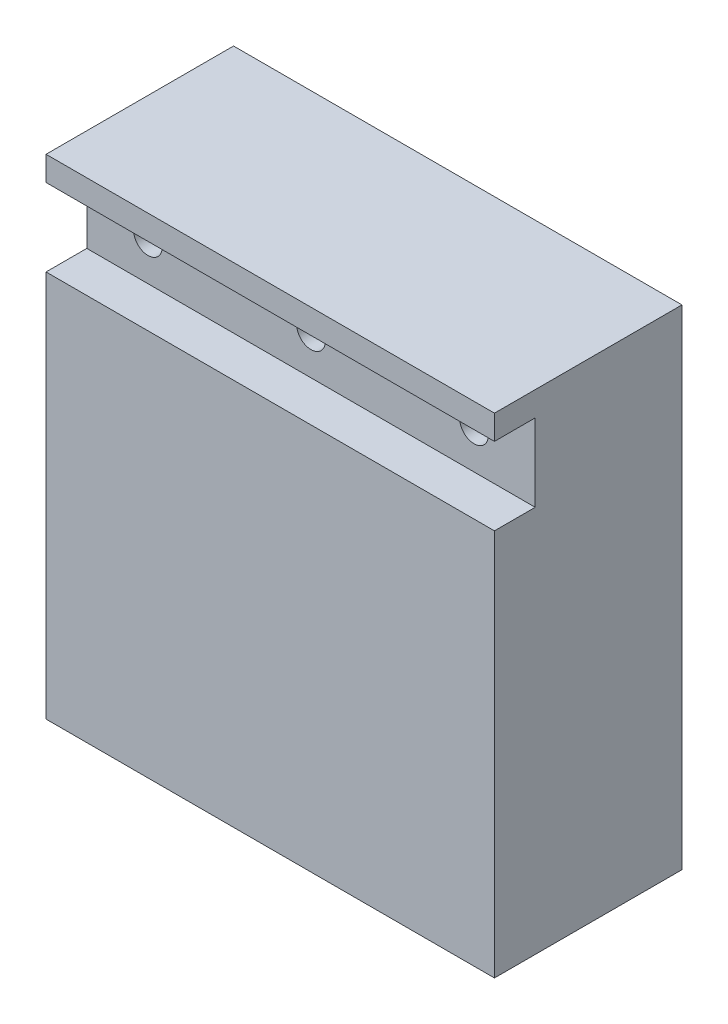
SolidWorks part; units mm, degrees
ref_plane "Front Plane" through (0, 0, 0) normal (0, 0, 1) x (1, 0, 0)
ref_plane "Top Plane" through (0, 0, 0) normal (0, 1, 0) x (1, 0, 0)
ref_plane "Right Plane" through (0, 0, 0) normal (1, 0, 0) x (0, 0, -1)
sketch "Sketch1" plane through (0, 0, 0) normal (1, 0, 0) x (0, 0, -1)
  line L1 (0, 0) -> (23, 0)
  line L2 (0, 0) -> (0, 60)
  line L3 (0, 60) -> (23, 60)
  line L4 (23, 0) -> (23, 60)
  dimension "D1" = 60
  dimension "D2" = 23
extrude "Boss-Extrude1" add sketch "Sketch1" along normal blind 55
sketch "Sketch2" plane through (0, 0, 0) normal (0, 0, 1) x (1, 0, 0)
  line L0 (55, 60) -> (55, 0) construction
  line L1 (0, 57) -> (55, 57)
  line L2 (0, 57) -> (0, 47.5)
  line L3 (0, 47.5) -> (55, 47.5)
  line L4 (55, 57) -> (55, 47.5)
  line L5 (55, 60) -> (0, 60) construction
  dimension "D1" = 9.5
  dimension "D2" = 3
  dimension "D3" = 55
extrude "Cut-Extrude1" cut sketch "Sketch2" against normal blind 5
sketch "Sketch3" plane through (0, 0, -5) normal (0, 0, 1) x (1, 0, 0)
  line L0 (0, 57) -> (0, 47.5) construction
  circle A0 centre (7.5, 52.25) radius 1.75
  circle A1 centre (27.5, 52.25) radius 1.75
  circle A2 centre (47.5, 52.25) radius 1.75
  point P8 (0, 52.25)
  dimension "D1" = 3.5
  dimension "D3" = 3.5
  dimension "D5" = 3.5
  dimension "D2" = 7.5
  dimension "D4" = 20
  dimension "D6" = 20
extrude "Cut-Extrude2" cut sketch "Sketch3" against normal blind 3
